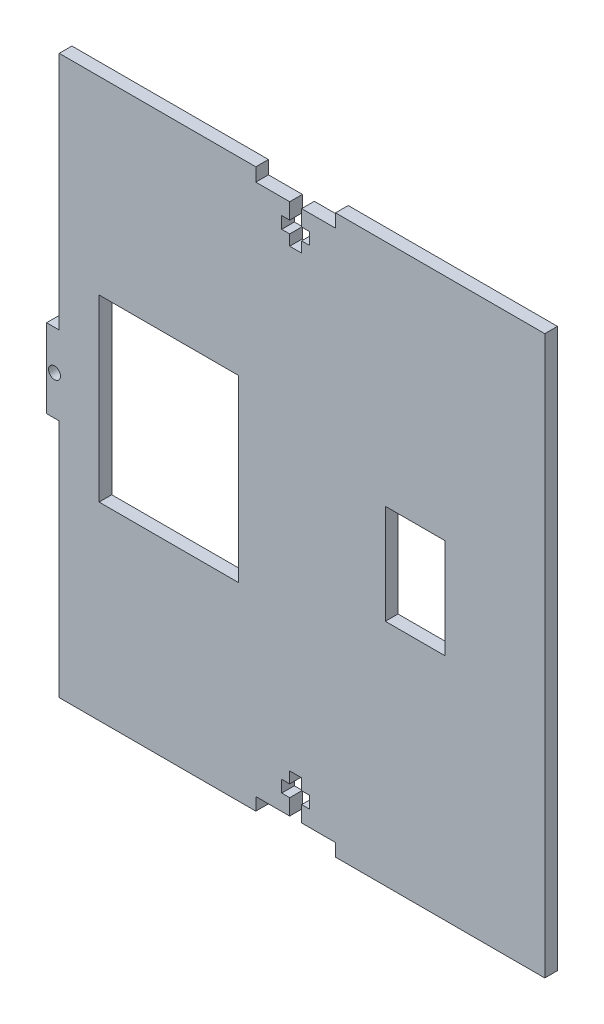
SolidWorks part; units mm, degrees
ref_plane "Front Plane" through (0, 0, 0) normal (0, 0, 1) x (1, 0, 0)
ref_plane "Top Plane" through (0, 0, 0) normal (0, 1, 0) x (1, 0, 0)
ref_plane "Right Plane" through (0, 0, 0) normal (1, 0, 0) x (0, 0, -1)
sketch "Sketch1" plane through (0, 0, 0) normal (0, 0, 1) x (1, 0, 0)
  line L1 (-62.5, 70) -> (62.5, 70)
  line L2 (-62.5, 70) -> (-62.5, -70)
  line L3 (-62.5, -70) -> (62.5, -70)
  line L4 (62.5, 70) -> (62.5, -70)
  line L5 (-62.5, 70) -> (62.5, -70) construction
  line L6 (-62.5, -70) -> (62.5, 70) construction
  point P0 (0, 0)
  dimension "D1" = 140
  dimension "D2" = 125
extrude "Boss-Extrude1" add sketch "Sketch1" along normal blind 3.18
sketch "Sketch2" plane through (0, 0, 3.18) normal (0, 0, 1) x (1, 0, 0)
  line L0 (-62.5, -70) -> (62.5, -70) construction
  line L5 (62.5, 0) -> (-87.9045, 0) construction
  line L6 (62.5, -70) -> (62.5, 70) construction
  line L12 (62.5, -70) -> (62.5, 70) construction
  line L38 (-62.5, 70) -> (-62.5, -70) construction
  line L39 (-62.5, 70) -> (-59.32, 70)
  line L40 (-62.5, 70) -> (-62.5, 9.875)
  line L41 (-62.5, 9.875) -> (-59.32, 9.875)
  line L42 (-59.32, 70) -> (-59.32, 9.875)
  line L43 (-62.5, -70) -> (-59.32, -70)
  line L44 (-62.5, -70) -> (-62.5, -9.875)
  line L45 (-62.5, -9.875) -> (-59.32, -9.875)
  line L46 (-59.32, -70) -> (-59.32, -9.875)
  line L47 (62.5, -9.875) -> (84.32, -9.875)
  line L48 (84.32, -73.9291) -> (84.32, -9.875)
  line L49 (62.5, -73.9291) -> (84.32, -73.9291)
  line L50 (62.5, -73.9291) -> (62.5, -9.875)
  line L51 (62.5, 10.125) -> (84.32, 10.125)
  line L52 (84.32, 75.125) -> (84.32, 10.125)
  line L53 (62.5, 75.125) -> (84.32, 75.125)
  line L54 (62.5, 75.125) -> (62.5, 10.125)
  line L70 (1.5, -66.82) -> (10, -66.82)
  line L71 (-10, -70) -> (10, -70)
  line L72 (-10, -70) -> (-10, -66.82)
  line L73 (-10, -66.82) -> (-1.5, -66.82)
  line L74 (10, -70) -> (10, -66.82)
  line L75 (-1.5, -62.82) -> (-3.5, -62.82)
  line L76 (-62.5, -70) -> (62.5, -70) construction
  line L77 (-1.5, -57) -> (1.5, -57)
  line L78 (-1.5, -57) -> (-1.5, -59.82)
  line L80 (1.5, -57) -> (1.5, -59.82)
  line L82 (0, -68.8059) -> (0, 72.0476) construction
  line L83 (3.5, -62.82) -> (1.5, -62.82)
  line L84 (3.5, -62.82) -> (3.5, -59.82)
  line L85 (3.5, -59.82) -> (1.5, -59.82)
  line L86 (-3.5, -62.82) -> (-3.5, -59.82)
  line L91 (-1.5, -59.82) -> (-3.5, -59.82)
  line L98 (-1.5, -62.82) -> (-1.5, -66.82)
  line L99 (1.5, -62.82) -> (1.5, -66.82)
  circle A0 centre (-60.5, 0) radius 1.5
  circle A1 centre (85.5, 0) radius 1.5
  point P6 (0, -57)
  point P67 (-32.11, -66.8097)
  point P72 (-32.3859, -61.3492)
  point P77 (-32.3859, -59.7197)
  dimension "D11" = 3
  dimension "D12" = 2
  dimension "D3" = 3
  dimension "D2" = 19.75
  dimension "D4" = 20
  dimension "D5" = 65
  dimension "D9" = 3.18
  dimension "D10" = 3.18
  dimension "D13" = 20
  dimension "D14" = 7
  dimension "D15" = 3.18
  dimension "D16" = 3
  dimension "D17" = 3
  dimension "D18" = 4
  dimension "D19" = 13
extrude "Cut-Extrude1" cut sketch "Sketch2" against normal through all
sketch "Sketch11" plane through (0, 0, 0) normal (0, 0, -1) x (-1, 0, 0)
  line L0 (-62.5, 70) -> (59.32, 70) construction
  line L1 (-10, 66.67) -> (-1.5, 66.67)
  line L2 (-10, 66.67) -> (-10, 70)
  line L3 (-10, 70) -> (10, 70)
  line L4 (10, 66.67) -> (10, 70)
  line L5 (0, 0) -> (0, 70) construction
  line L6 (-62.5, 70) -> (59.32, 70) construction
  line L7 (-1.5, 62.67) -> (-1.5, 66.67)
  line L8 (-1.5, 57) -> (1.5, 57)
  line L9 (-1.5, 57) -> (-1.5, 59.67)
  line L11 (1.5, 57) -> (1.5, 59.67)
  line L12 (1.5, 66.67) -> (10, 66.67)
  line L14 (-3.5, 59.67) -> (-1.5, 59.67)
  line L15 (-3.5, 59.67) -> (-3.5, 62.67)
  line L16 (-3.5, 62.67) -> (-1.5, 62.67)
  line L17 (3.5, 59.67) -> (3.5, 62.67)
  line L25 (1.5, 62.67) -> (1.5, 66.67)
  line L26 (1.5, 59.67) -> (3.5, 59.67)
  line L28 (1.5, 62.67) -> (3.5, 62.67)
  point P8 (30.4223, 62.891)
  point P15 (30.4223, 62.1751)
  dimension "D1" = 20
  dimension "D2" = 3
  dimension "D3" = 3
  dimension "D4" = 13
  dimension "D5" = 7
  dimension "D6" = 4
sketch "Sketch12" plane through (0, 0, 0) normal (0, 0, -1) x (-1, 0, 0)
  line L0 (-62.5, 0) -> (139.8215, 0) construction
  line L1 (14.32, -22.5) -> (49.32, -22.5)
  line L2 (14.32, -22.5) -> (14.32, 22.5)
  line L3 (14.32, 22.5) -> (49.32, 22.5)
  line L4 (49.32, -22.5) -> (49.32, 22.5)
  line L5 (14.32, -22.5) -> (49.32, 22.5) construction
  line L6 (14.32, 22.5) -> (49.32, -22.5) construction
  line L7 (-62.5, -70) -> (-62.5, 70) construction
  line L8 (59.32, 10.5071) -> (59.32, 67.1771) construction
  point P0 (31.82, 0)
  point P10 (0, 0)
  dimension "D1" = 45
  dimension "D2" = 35
  dimension "D3" = 10
extrude "Cut-Extrude6" cut sketch "Sketch12" against normal through all
sketch "Sketch13" plane through (0, 0, 0) normal (0, 0, -1) x (-1, 0, 0)
  line L0 (-62.5, 0) -> (56.6087, 0) construction
  line L1 (-37.5, -12.5) -> (-22.5, -12.5)
  line L2 (-37.5, -12.5) -> (-37.5, 12.5)
  line L3 (-37.5, 12.5) -> (-22.5, 12.5)
  line L4 (-22.5, -12.5) -> (-22.5, 12.5)
  line L5 (-37.5, -12.5) -> (-22.5, 12.5) construction
  line L6 (-37.5, 12.5) -> (-22.5, -12.5) construction
  line L7 (-62.5, -70) -> (-62.5, 70) construction
  point P0 (-30, 0)
  dimension "D1" = 25
  dimension "D2" = 15
  dimension "D3" = 25
extrude "Cut-Extrude7" cut sketch "Sketch13" against normal through all
extrude "Cut-Extrude11" cut sketch "Sketch11" against normal blind 10
equation "\"sheet\"= 3.18mm"
equation "\"screwD\"= 2.94mm"
equation "\"tabW\"= 20mm"
equation "\"nut2\"= 6.5mm"
